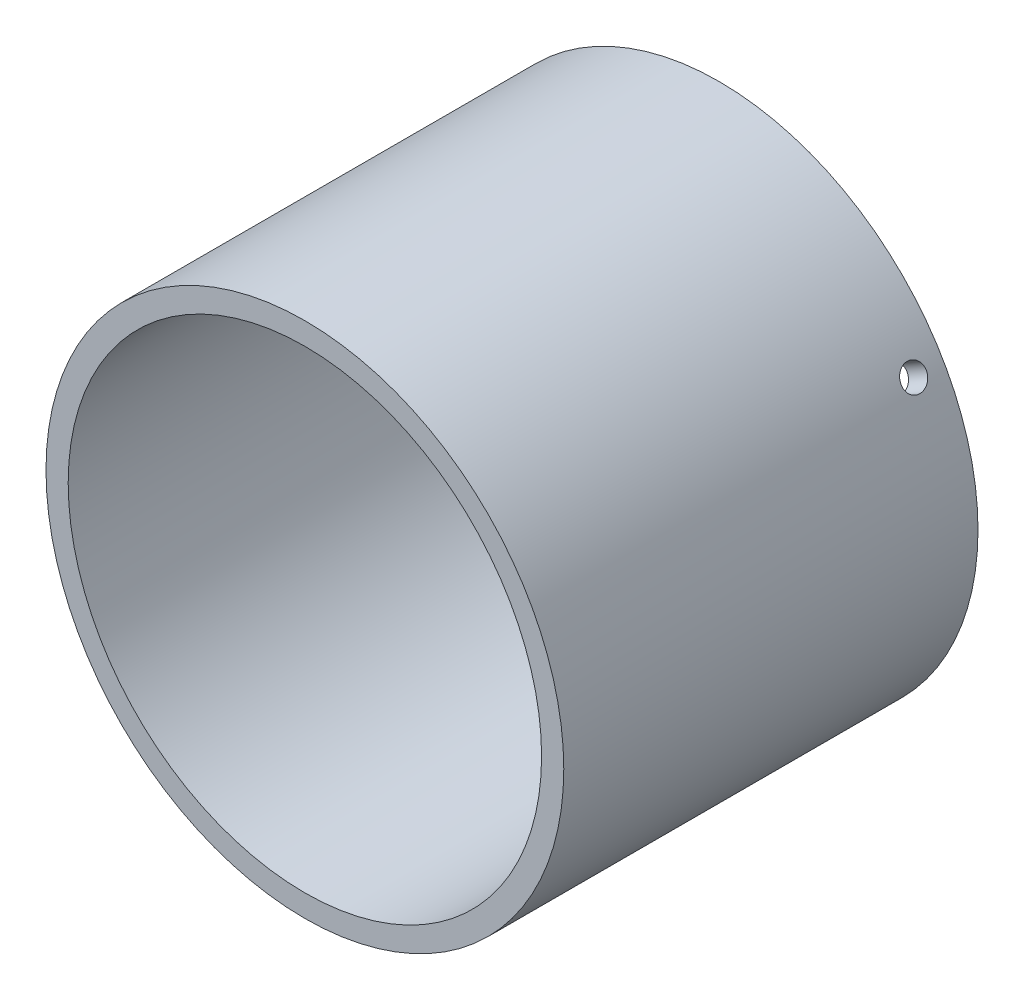
SolidWorks part; units mm, degrees
ref_plane "Plan1" through (0, 0, 0) normal (0, 0, 1) x (1, 0, 0)
ref_plane "Plan2" through (0, 0, 0) normal (0, 1, 0) x (1, 0, 0)
ref_plane "Plan3" through (0, 0, 0) normal (1, 0, 0) x (0, 0, -1)
sketch "Esquisse1" plane through (0, 0, 0) normal (0, 0, 1) x (1, 0, 0)
  circle A0 centre (0, 0) radius 32
  circle A1 centre (0, 0) radius 35
  dimension "D1" = 64
  dimension "D2" = 70
extrude "Base-Extrusion" add sketch "Esquisse1" along normal blind 56
sketch "Esquisse2" plane through (0, 0, 0) normal (0, 1, 0) x (1, 0, 0)
  line L0 (0, 0) -> (0, -4) construction
  line L1 (0, -56) -> (0, 0) construction
  circle A0 centre (0, -4) radius 1.7
  dimension "D2" = 3.4
  dimension "D1" = 4
extrude "Enlèv. mat.-Extru.1" cut sketch "Esquisse2" against normal through all
pattern_circular "Répétition circulaire1" count 3 every 120
